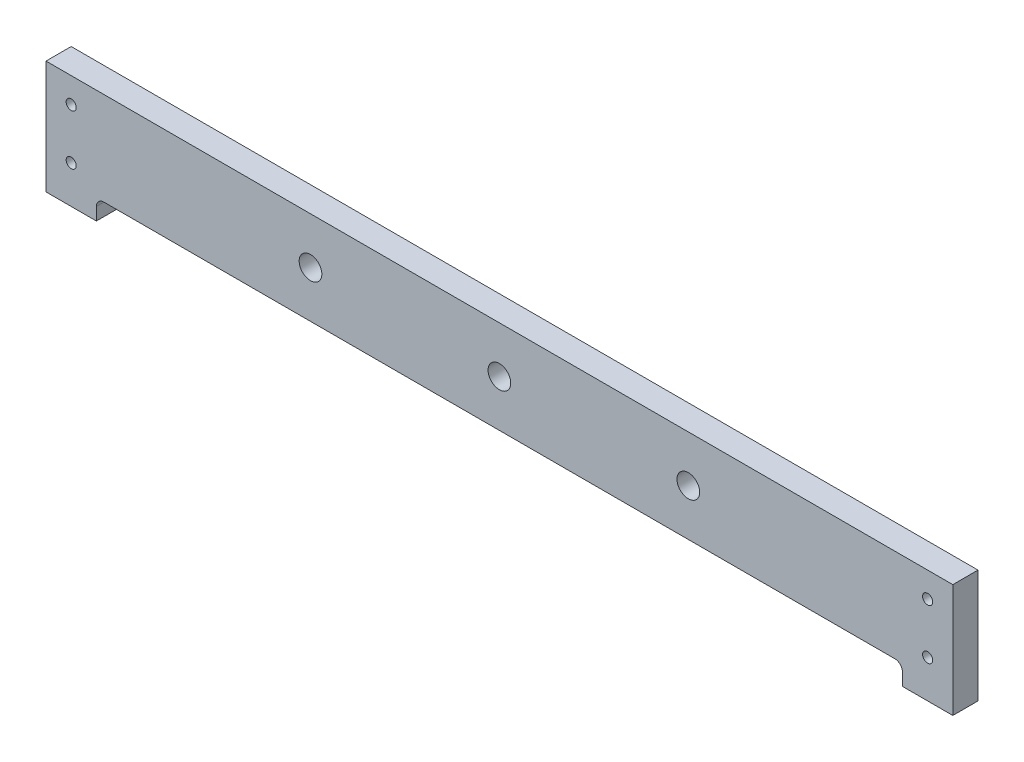
SolidWorks part; units mm, degrees
ref_plane "Front Plane" through (0, 0, 0) normal (0, 0, 1) x (1, 0, 0)
ref_plane "Top Plane" through (0, 0, 0) normal (0, 1, 0) x (1, 0, 0)
ref_plane "Right Plane" through (0, 0, 0) normal (1, 0, 0) x (0, 0, -1)
sketch "Sketch1" plane through (0, 0, 0) normal (0, 0, 1) x (1, 0, 0)
  line L0 (0, 0) -> (360, 0)
  line L1 (360, 0) -> (360, -45)
  line L2 (360, -45) -> (340, -45)
  line L3 (340, -45) -> (340, -40)
  line L4 (0, 0) -> (0, -45)
  line L5 (0, -45) -> (20, -45)
  line L6 (20, -45) -> (20, -40)
  line L7 (23, -37) -> (337, -37)
  arc A0 (23, -37) -> (20, -40) centre (23, -40) ccw
  arc A1 (340, -40) -> (337, -37) centre (337, -40) ccw
  circle A2 centre (350, -10) radius 2
  circle A3 centre (350, -30) radius 2
  circle A4 centre (10, -10) radius 2
  circle A5 centre (10, -30.0045) radius 2
  circle A6 centre (180, -18.5) radius 4.5
  circle A7 centre (255, -18.5) radius 4.5
  circle A8 centre (105, -18.5) radius 4.5
  point P11 (20, -37)
  point P28 (0, 0)
  point P29 (180, 0)
  point P30 (0, 0)
  point P31 (0, 0)
  point P32 (0, 0)
  dimension "D6" = 3
  dimension "D7" = 3
  dimension "D13" = 4
  dimension "D14" = 4
  dimension "D15" = 4
  dimension "D16" = 4
  dimension "D21" = 9
  dimension "D23" = 9
  dimension "D24" = 9
  dimension "D1" = 360
  dimension "D2" = 45
  dimension "D3" = 20
  dimension "D4" = 8
  dimension "D5" = 20
  dimension "D8" = 45
  dimension "D9" = 10
  dimension "D10" = 10
  dimension "D11" = 10
  dimension "D12" = 20
  dimension "D17" = 10
  dimension "D18" = 10
  dimension "D19" = 20.0045
  dimension "D20" = 10
  dimension "D22" = 18.5
  dimension "D25" = 75
  dimension "D26" = 75
extrude "Boss-Extrude1" add sketch "Sketch1" along normal blind 10
